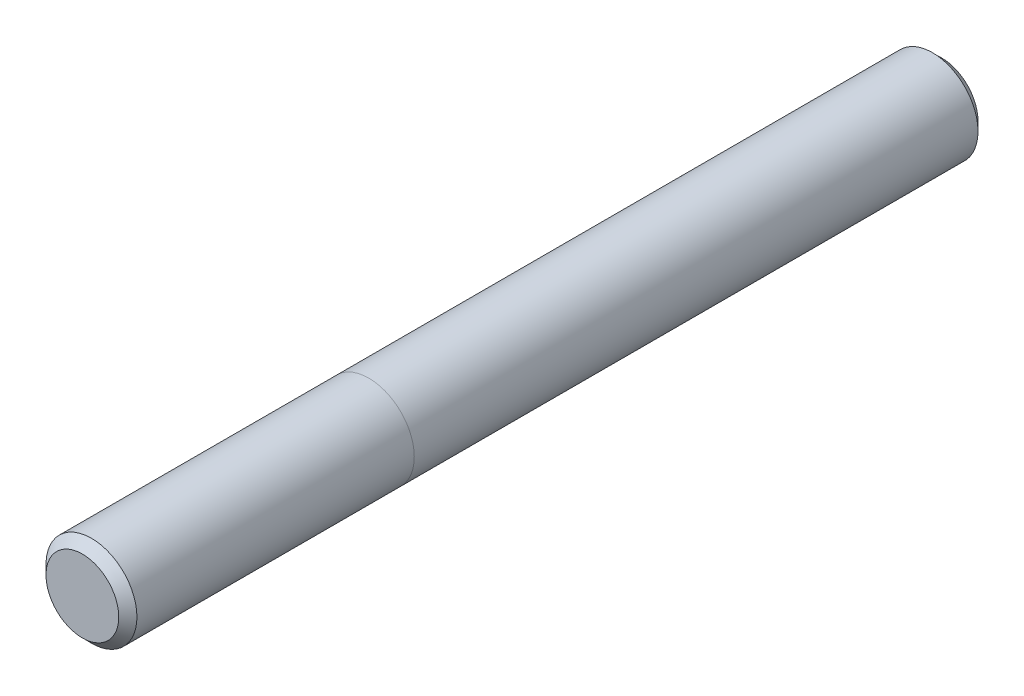
SolidWorks part; units mm, degrees
material "Plain Carbon Steel"
ref_plane "Front" through (0, 0, 0) normal (0, 0, 1) x (1, 0, 0)
ref_plane "Top" through (0, 0, 0) normal (0, 1, 0) x (1, 0, 0)
ref_plane "Right" through (0, 0, 0) normal (1, 0, 0) x (0, 0, -1)
sketch "Sketch1" plane through (0, 0, 0) normal (0, 0, 1) x (1, 0, 0)
  circle A0 centre (0, 0) radius 7.9375
  dimension "Diameter" = 15.875
sketch "Sketch2" plane through (0, 0, 0) normal (1, 0, 0) x (0, 0, -1)
  line L0 (-75, 0) -> (75, 0) construction
  line L1 (-24.2, 7.9375) -> (-24.2, -7.9375) construction
  line L2 (8.7312, 0) -> (-8.7312, 0) construction
  line L3 (24.2, 7.9375) -> (24.2, -7.9375) construction
  line L4 (-75, 7.9375) -> (-75, -7.9375) construction
  line L5 (75, 7.9375) -> (75, -7.9375) construction
  point P3 (-24.2, 0)
  point P8 (0, 0)
  point P9 (24.2, 0)
  point P15 (-75, 0)
  point P18 (75, 0)
  dimension "D1" = 15.875
  dimension "Length" = 150
  dimension "D2" = 50.8
  dimension "D3" = 50.8
sketch "Sketch3" plane through (0, 0, 0) normal (0, 0, 1) x (1, 0, 0)
  circle A0 centre (0, 0) radius 7.9375
  dimension "D1" = 15.875
extrude "Boss-Extrude1" add sketch "Sketch3" along normal mid plane 150
chamfer "Chamfer1" distance 1.5875 angle 45 2 edges at (7.9375, 0, -75) (7.9375, 0, 75)
sketch "Sketch5" plane through (0, 0, 0) normal (0, 1, 0) x (1, 0, 0)
  line L0 (-7.9375, -25) -> (7.9375, -25)
  line L1 (-7.9375, 73.4125) -> (-7.9375, -73.4125) construction
  line L2 (7.9375, -73.4125) -> (7.9375, 73.4125) construction
  line L4 (-6.35, -75) -> (6.35, -75) construction
  dimension "D1" = 50
split line "Split Line1"
equation "\"D1@Sketch3\" = \"Diameter@Sketch1\""
equation "\"D1@Boss-Extrude1\" = \"Length@Sketch2\""
equation "\"D1@Chamfer1\" = \"Diameter@Sketch1\" * .1"
equation "\"D1@Sketch2\" = \"Diameter@Sketch1\""
